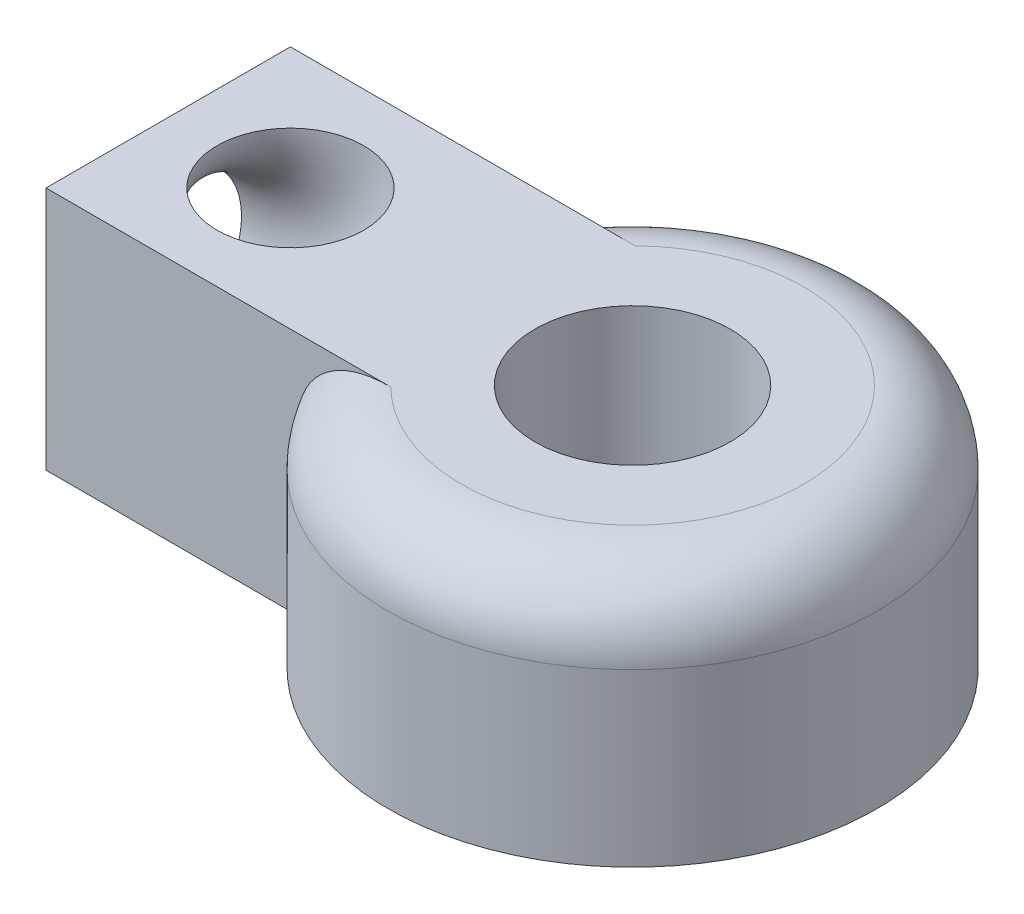
SolidWorks part; units mm, degrees
ref_plane "Front Plane" through (0, 0, 0) normal (0, 0, 1) x (1, 0, 0)
ref_plane "Top Plane" through (0, 0, 0) normal (0, 1, 0) x (1, 0, 0)
ref_plane "Right Plane" through (0, 0, 0) normal (1, 0, 0) x (0, 0, -1)
sketch "Sketch1" plane through (0, 0, 0) normal (0, 1, 0) x (1, 0, 0)
  circle A0 centre (0, 0) radius 4
  circle A1 centre (0, 0) radius 10
extrude "Boss-Extrude1" add sketch "Sketch1" along normal blind 10
sketch "Sketch2" plane through (0, 10, 0) normal (0, 1, 0) x (1, 0, 0)
  line L0 (0, 0) -> (-4, 0)
  line L1 (-4, -5) -> (-19, -5)
  line L2 (-4, -5) -> (-4, 5)
  line L3 (-4, 5) -> (-19, 5)
  line L4 (-19, -5) -> (-19, 5)
  circle A0 centre (0, 0) radius 10 construction
  circle A1 centre (0, 0) radius 4 construction
  point P0 (-10, 0)
  point P14 (-4, 0)
  circle M1 centre (0, 0) radius 10
extrude "Boss-Extrude2" add sketch "Sketch2" against normal blind 10 contours L4 L1 L3 M1
sketch "Sketch3" plane through (-19, 0, 0) normal (-1, 0, 0) x (0, 0, 1)
  line L0 (0, 5) -> (0, 0) construction
  line L1 (5, 10) -> (-5, 10) construction
  circle A1 centre (0, 5) radius 3
  point P0 (0, 5)
revolve "Cut-Revolve1" cut sketch "Sketch3" angle 360 about L1
fillet "Fillet1" radius 3 1 edges at (10, 10, 0)
